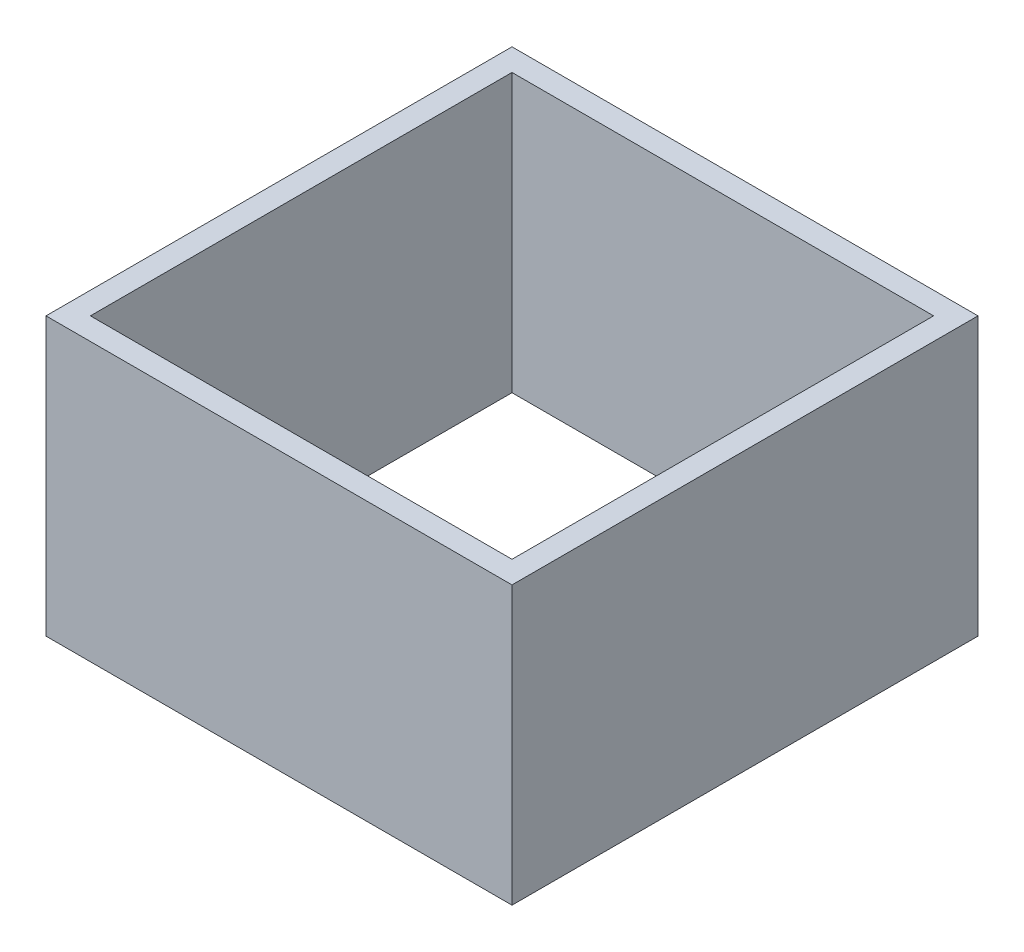
SolidWorks part; units mm, degrees
ref_plane "Front Plane" through (0, 0, 0) normal (0, 0, 1) x (1, 0, 0)
ref_plane "Top Plane" through (0, 0, 0) normal (0, 1, 0) x (1, 0, 0)
ref_plane "Right Plane" through (0, 0, 0) normal (1, 0, 0) x (0, 0, -1)
sketch "Sketch1" plane through (0, 0, 0) normal (0, 1, 0) x (1, 0, 0)
  line L0 (-21, -21) -> (-21, 21)
  line L1 (19, -19) -> (-19, -19)
  line L2 (19, -19) -> (19, 19)
  line L3 (19, 19) -> (-19, 19)
  line L4 (-19, -19) -> (-19, 19)
  line L5 (19, -19) -> (-19, 19) construction
  line L6 (19, 19) -> (-19, -19) construction
  line L7 (21, 21) -> (-21, 21)
  line L8 (21, -21) -> (21, 21)
  line L9 (21, -21) -> (-21, -21)
  point P0 (0, 0)
  dimension "D1" = 38
  dimension "D2" = 2
extrude "Boss-Extrude1" add sketch "Sketch1" along normal blind 25
